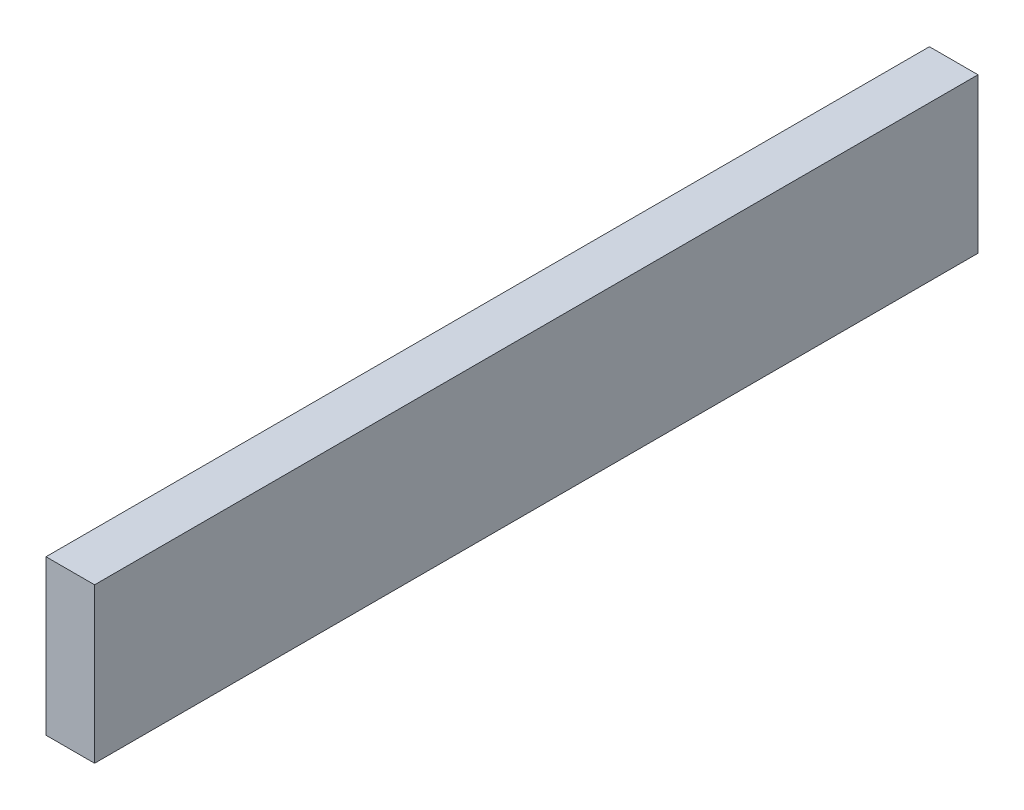
SolidWorks part; units mm, degrees
ref_plane "Face" through (0, 0, 0) normal (0, 0, 1) x (1, 0, 0)
ref_plane "Dessus" through (0, 0, 0) normal (0, 1, 0) x (1, 0, 0)
ref_plane "Droite" through (0, 0, 0) normal (1, 0, 0) x (0, 0, -1)
sketch "Esquisse1" plane through (0, 0, 0) normal (0, 1, 0) x (1, 0, 0)
  line L1 (0, 0) -> (22, 0)
  line L2 (0, 0) -> (0, 400)
  line L3 (0, 400) -> (22, 400)
  line L4 (22, 0) -> (22, 400)
  dimension "D1" = 400
  dimension "D2" = 22
extrude "Extrusion1" add sketch "Esquisse1" along normal blind 70
